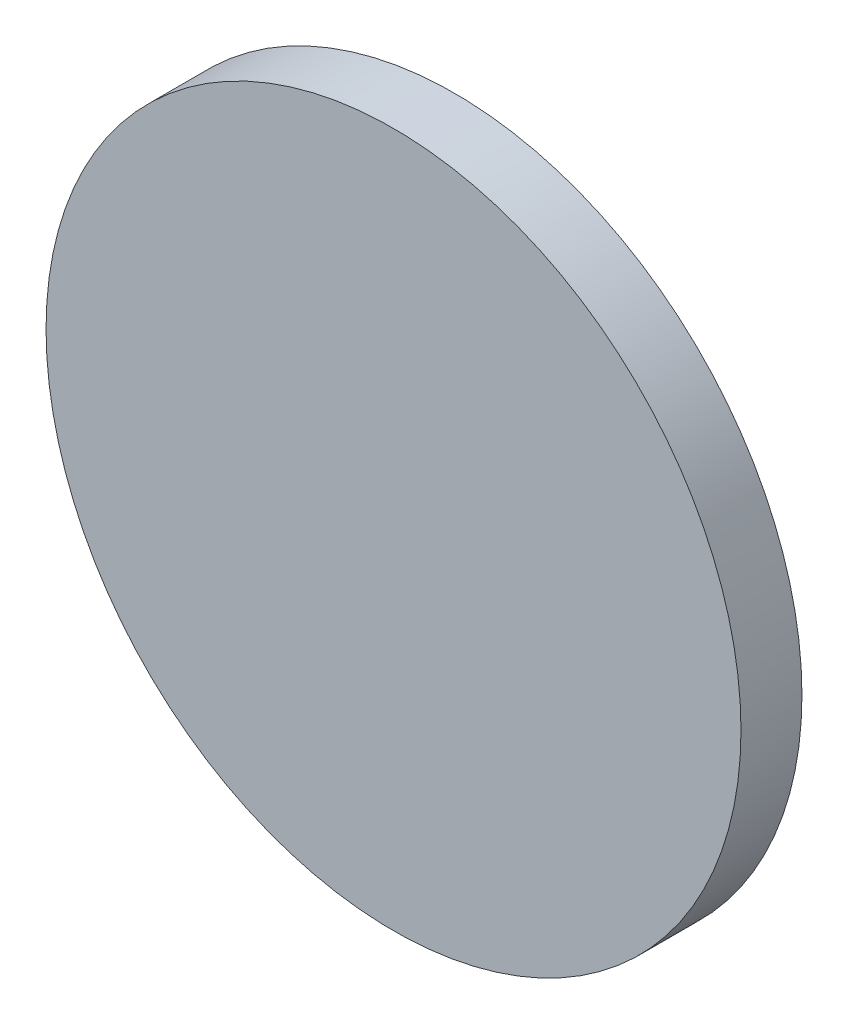
SolidWorks part; units mm, degrees
ref_plane "Front Plane" through (0, 0, 0) normal (0, 0, 1) x (1, 0, 0)
ref_plane "Top Plane" through (0, 0, 0) normal (0, 1, 0) x (1, 0, 0)
ref_plane "Right Plane" through (0, 0, 0) normal (1, 0, 0) x (0, 0, -1)
sketch "Sketch1" plane through (0, 0, 0) normal (0, 0, 1) x (1, 0, 0)
  circle A0 centre (0, 0) radius 56.9932
extrude "Boss-Extrude1" add sketch "Sketch1" along normal blind 10
